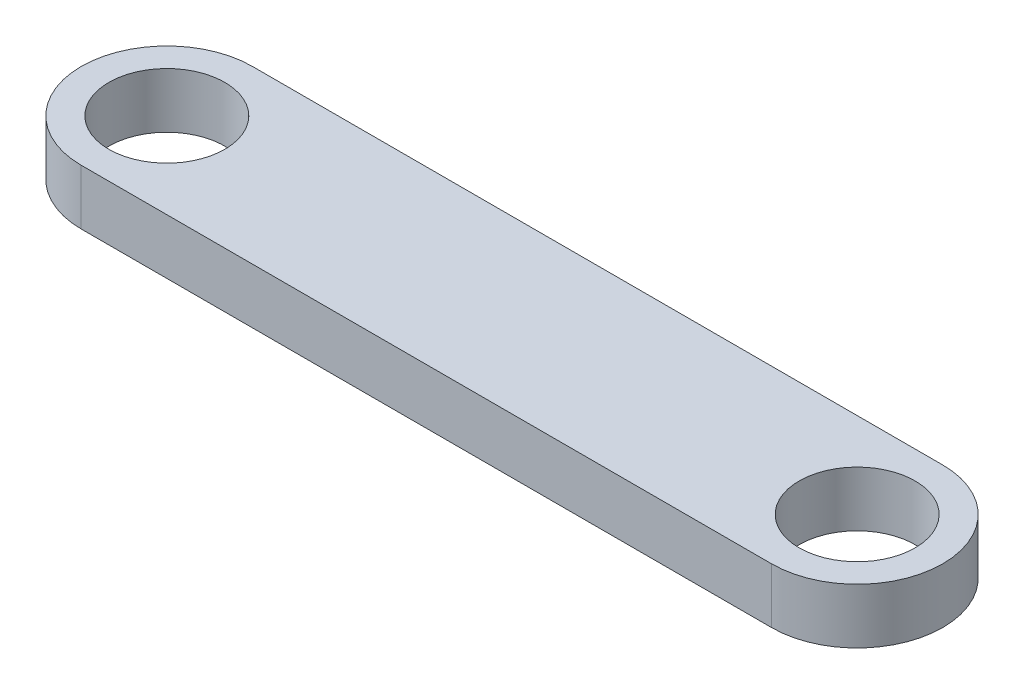
SolidWorks part; units mm, degrees
ref_plane "Front" through (0, 0, 0) normal (0, 0, 1) x (1, 0, 0)
ref_plane "Top" through (0, 0, 0) normal (0, 1, 0) x (1, 0, 0)
ref_plane "Right" through (0, 0, 0) normal (1, 0, 0) x (0, 0, -1)
sketch "Sketch1" plane through (0, 0, 0) normal (0, 1, 0) x (1, 0, 0)
  line L6 (-12.5, 3.1) -> (12.5, 3.1)
  line L7 (12.5, -3.1) -> (-12.5, -3.1)
  circle A0 centre (-12.5, 0) radius 2.1
  circle A1 centre (12.5, 0) radius 2.1
  arc A2 (-12.5, -3.1) -> (-12.5, 3.1) centre (-12.5, 0) cw
  arc A3 (12.5, 3.1) -> (12.5, -3.1) centre (12.5, 0) cw
extrude "Boss-Extrude1" add sketch "Sketch1" along normal blind 2
